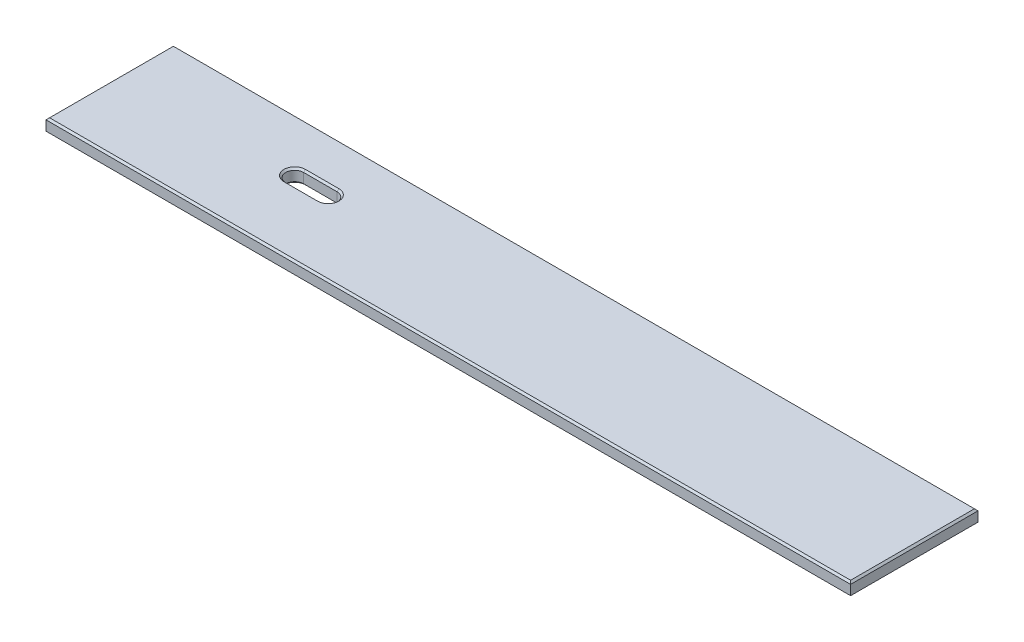
SolidWorks part; units mm, degrees
material "Oak"
ref_plane "Front Plane" through (0, 0, 0) normal (0, 0, 1) x (1, 0, 0)
ref_plane "Top Plane" through (0, 0, 0) normal (0, 1, 0) x (1, 0, 0)
ref_plane "Right Plane" through (0, 0, 0) normal (1, 0, 0) x (0, 0, -1)
sketch "Sketch1" plane through (0, 0, 0) normal (0, 1, 0) x (1, 0, 0)
  line L0 (271.5069, 92.856) -> (271.5069, 194.4655) construction
  line L1 (0, 0) -> (1143, 0)
  line L2 (0, 0) -> (0, 180.975)
  line L3 (0, 180.975) -> (1143, 180.975)
  line L4 (1143, 0) -> (1143, 180.975)
  line L6 (247.7262, 118.256) -> (295.2877, 118.256)
  line L8 (247.7262, 92.856) -> (295.2877, 92.856)
  arc A4 (295.2877, 92.856) -> (295.2877, 118.256) centre (295.2877, 105.556) ccw
  arc A5 (247.7262, 118.256) -> (247.7262, 92.856) centre (247.7262, 105.556) ccw
  point P14 (295.2877, 118.256)
  dimension "D7" = 25.4
  dimension "D1" = 180.975
  dimension "D2" = 1143
  dimension "D3" = 47.5615
  dimension "D4" = 105.556
  dimension "D5" = 295.2877
extrude "Boss-Extrude1" add sketch "Sketch1" along normal blind 19.05
chamfer "Chamfer1" distance 2.54 angle 45 8 edges at (571.5, 19.05, -180.975) (1143, 19.05, -90.4875) (571.5, 19.05, 0) (0, 19.05, -90.4875) (271.5069, 19.05, -118.256) (271.5069, 19.05, -92.856) (235.0262, 19.05, -105.556) (307.9877, 19.05, -105.556)
chamfer "Chamfer2" distance 2.54 angle 45 8 edges at (271.5069, 0, -118.256) (271.5069, 0, -92.856) (571.5, 0, 0) (1143, 0, -90.4875) (571.5, 0, -180.975) (0, 0, -90.4875) (235.0262, 0, -105.556) (307.9877, 0, -105.556)
